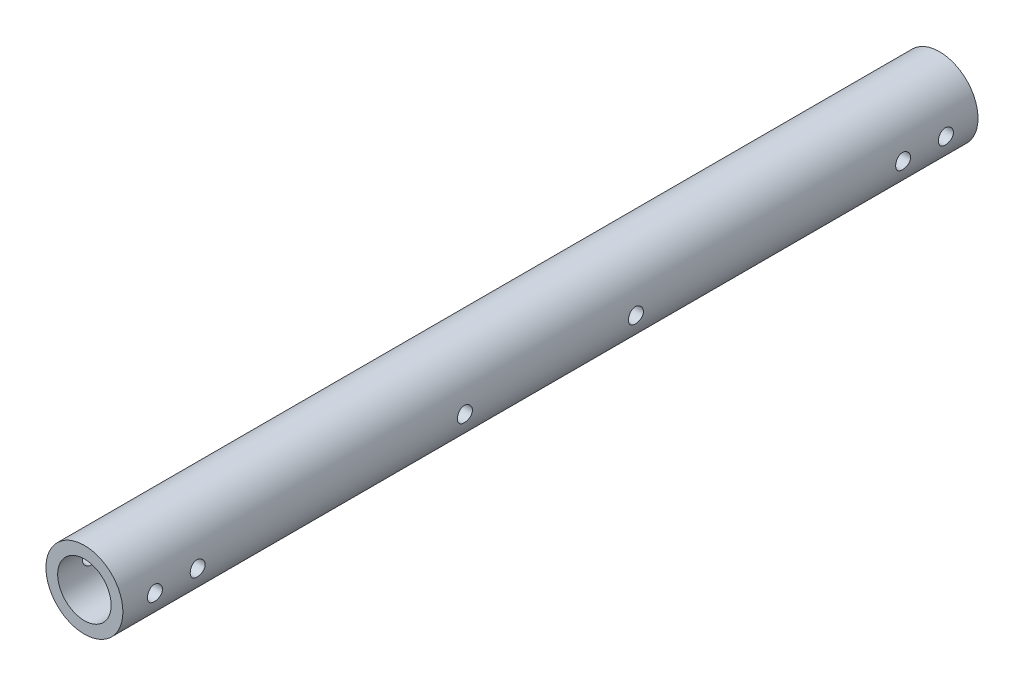
SolidWorks part; units mm, degrees
material "ﾎﾟﾘ塩化ﾋﾞﾆﾙ(PVC)硬質"
ref_plane "正面(Front)" through (0, 0, 0) normal (0, 0, 1) x (1, 0, 0)
ref_plane "平面(Top)" through (0, 0, 0) normal (0, 1, 0) x (1, 0, 0)
ref_plane "右側面(Right)" through (0, 0, 0) normal (1, 0, 0) x (0, 0, -1)
sketch "ｽｹｯﾁ1" plane through (0, 0, 0) normal (0, 0, 1) x (1, 0, 0)
  circle A0 centre (0, 0) radius 9
  circle A1 centre (0, 0) radius 6.25
  dimension "D1" = 18
  dimension "D2" = 12.5
extrude "ﾎﾞｽ - 押し出し1" add sketch "ｽｹｯﾁ1" along normal blind 200
sketch "ｽｹｯﾁ2" plane through (0, 0, 0) normal (1, 0, 0) x (0, 0, -1)
  line L0 (0, 0) -> (-200, 0) construction
  line L1 (0, -9) -> (0, 9) construction
  line L2 (-200, 9) -> (-200, -9) construction
  line L3 (-100, 0) -> (-100, 43.8276) construction
  circle A0 centre (-7.5, 0) radius 1.75
  circle A1 centre (-192.5, 0) radius 1.75
  circle A2 centre (-80, 0) radius 1.75
  circle A3 centre (-120, 0) radius 1.75
  circle A4 centre (-17.5, 0) radius 1.75
  circle A5 centre (-182.5, 0) radius 1.75
  dimension "D2" = 7.5
  dimension "D3" = 3.5
  dimension "D4" = 3.5
  dimension "D5" = 40
  dimension "D6" = 10
  dimension "D1" = 7.5
extrude "ｶｯﾄ - 押し出し1" cut sketch "ｽｹｯﾁ2" against normal through all both and the other way through all
